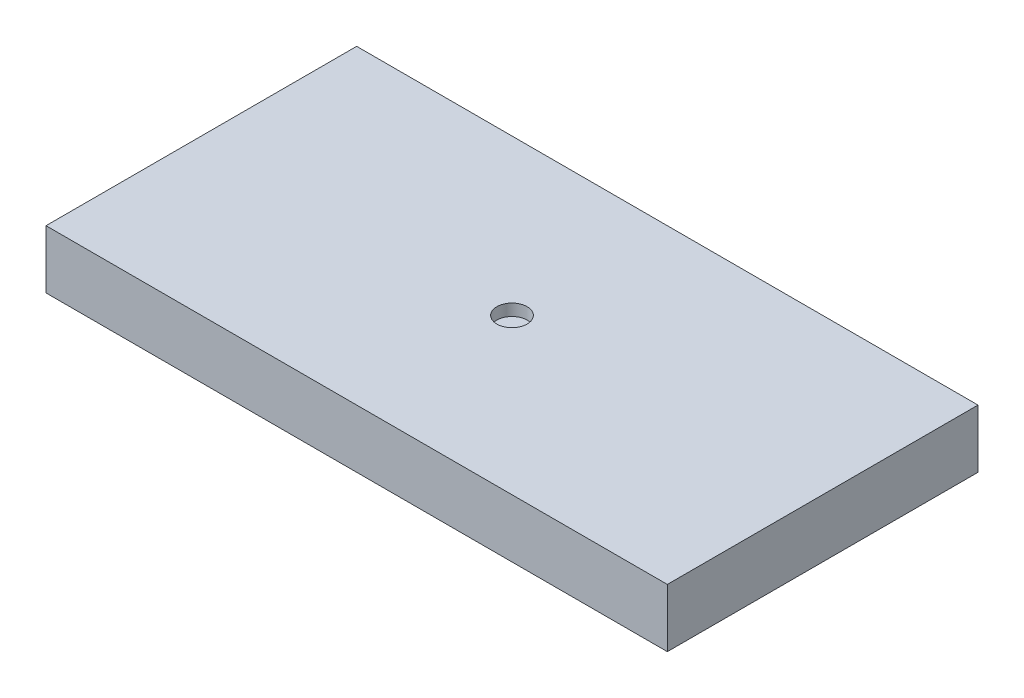
SolidWorks part; units mm, degrees
ref_plane "Front Plane" through (0, 0, 0) normal (0, 0, 1) x (1, 0, 0)
ref_plane "Top Plane" through (0, 0, 0) normal (0, 1, 0) x (1, 0, 0)
ref_plane "Right Plane" through (0, 0, 0) normal (1, 0, 0) x (0, 0, -1)
sketch "Sketch1" plane through (0, 0, 0) normal (0, 1, 0) x (1, 0, 0)
  line L1 (-20.32, -10.16) -> (20.32, -10.16)
  line L2 (-20.32, -10.16) -> (-20.32, 10.16)
  line L3 (-20.32, 10.16) -> (20.32, 10.16)
  line L4 (20.32, -10.16) -> (20.32, 10.16)
  line L5 (-20.32, -10.16) -> (20.32, 10.16) construction
  line L6 (-20.32, 10.16) -> (20.32, -10.16) construction
  point P0 (0, 0)
  dimension "D1" = 20.32
  dimension "D2" = 40.64
extrude "Boss-Extrude2" add sketch "Sketch1" along normal blind 3.81
sketch "Sketch2" plane through (0, 3.81, 0) normal (0, 1, 0) x (1, 0, 0)
  circle A0 centre (0, 0) radius 0.9882
extrude "Cut-Extrude1" cut sketch "Sketch2" against normal blind 0.762
